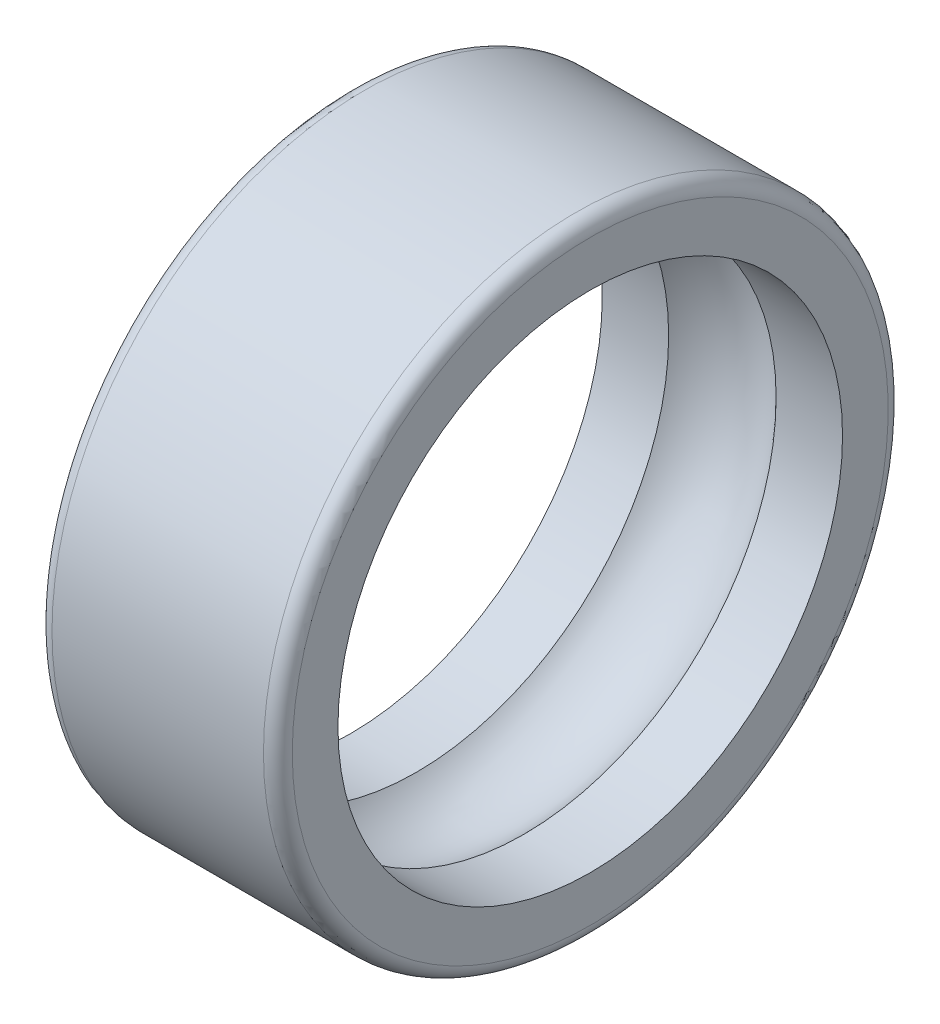
SolidWorks part; units mm, degrees
ref_plane "Plan1" through (0, 0, 0) normal (0, 0, 1) x (1, 0, 0)
ref_plane "Plan2" through (0, 0, 0) normal (0, 1, 0) x (1, 0, 0)
ref_plane "Plan3" through (0, 0, 0) normal (1, 0, 0) x (0, 0, -1)
sketch "Esquisse1" plane through (0, 0, 0) normal (0, 0, 1) x (1, 0, 0)
  line L0 (0, 5.25) -> (1.382, 5.25) construction
  line L1 (0, 5.25) -> (0, 6.5) construction
  line L2 (0, 6.5) -> (5, 6.5) construction
  line L3 (5, 5.25) -> (5, 6.5) construction
  line L4 (3.618, 5.25) -> (5, 5.25) construction
  line L5 (0, 5.25) -> (1.382, 5.25)
  line L6 (0, 5.25) -> (0, 6.5)
  line L7 (0, 6.5) -> (5, 6.5)
  line L8 (5, 5.25) -> (5, 6.5)
  line L9 (3.618, 5.25) -> (5, 5.25)
  line L10 (0, 0) -> (9.2186, 0) construction
  line L11 (0, 0) -> (24.3288, 0) construction
  circle A0 centre (2.5, 4.25) radius 1.5 construction
  arc A1 (3.618, 5.25) -> (1.382, 5.25) centre (2.5, 4.25) ccw
revolve "Base-Révolution" add sketch "Esquisse1" angle 360 about L10
fillet "Congé1" radius 0.3
